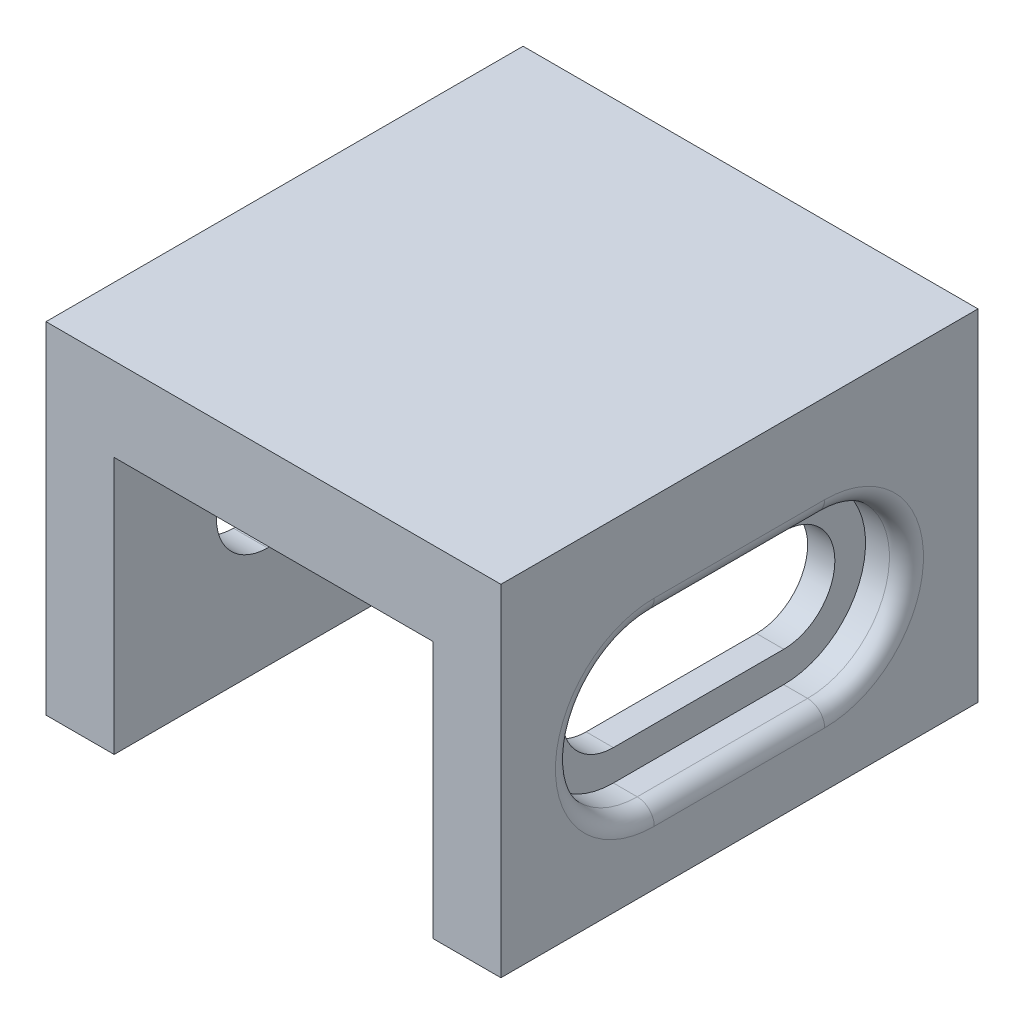
SolidWorks part; units mm, degrees
ref_plane "Front Plane" through (0, 0, 0) normal (0, 0, 1) x (1, 0, 0)
ref_plane "Top Plane" through (0, 0, 0) normal (0, 1, 0) x (1, 0, 0)
ref_plane "Right Plane" through (0, 0, 0) normal (1, 0, 0) x (0, 0, -1)
sketch "Sketch1" plane through (0, 0, 0) normal (0, 1, 0) x (1, 0, 0)
  line L1 (0, 0) -> (26.7, 0)
  line L2 (0, 0) -> (0, 28)
  line L3 (0, 28) -> (26.7, 28)
  line L4 (26.7, 0) -> (26.7, 28)
  dimension "D1" = 26.7
  dimension "D2" = 28
extrude "Boss-Extrude1" add sketch "Sketch1" along normal blind 20
sketch "Sketch2" plane through (0, 0, 0) normal (-1, 0, 0) x (0, 0, 1)
  line L0 (0, 20) -> (0, 0) construction
  line L1 (-28, 0) -> (0, 0) construction
  line L2 (-28, 20) -> (-28, 0) construction
  line L4 (-19, 12) -> (-9, 12)
  line L6 (-19, 6) -> (-9, 6)
  arc A0 (-9, 6) -> (-9, 12) centre (-9, 9) ccw
  arc A1 (-19, 12) -> (-19, 6) centre (-19, 9) ccw
  dimension "D1" = 6
  dimension "D4" = 9
  dimension "D6" = 6
  dimension "D2" = 9
  dimension "D5" = 9
extrude "Cut-Extrude1" cut sketch "Sketch2" against normal blind 27.5
sketch "Sketch3" plane through (0, 0, 0) normal (-1, 0, 0) x (0, 0, 1)
  line L1 (-19, 13.8) -> (-9, 13.8)
  line L3 (-19, 4.2) -> (-9, 4.2)
  arc A0 (-9, 4.2) -> (-9, 13.8) centre (-9, 9) ccw
  arc A1 (-19, 13.8) -> (-19, 4.2) centre (-19, 9) ccw
  point P1 (0, 0)
  point P4 (0, 0)
  point P5 (0, 0)
  dimension "D1" = 4.8
extrude "Cut-Extrude2" cut sketch "Sketch3" against normal blind 2
sketch "Sketch4" plane through (26.7, 0, 0) normal (1, 0, 0) x (0, 0, -1)
  line L1 (9, 13.8) -> (19, 13.8)
  line L3 (9, 4.2) -> (19, 4.2)
  arc A0 (9, 13.8) -> (9, 4.2) centre (9, 9) ccw
  arc A1 (19, 4.2) -> (19, 13.8) centre (19, 9) ccw
  dimension "D1" = 4.8
extrude "Cut-Extrude3" cut sketch "Sketch4" against normal blind 2.4
sketch "Sketch5" plane through (0, 0, 0) normal (0, 1, 0) x (1, 0, 0)
  line L0 (26.7, 28) -> (0, 28) construction
  line L1 (4, 28) -> (22.7, 28)
  line L2 (4, 28) -> (4, 0)
  line L3 (4, 0) -> (22.7, 0)
  line L4 (22.7, 28) -> (22.7, 0)
  line L5 (0, 0) -> (26.7, 0) construction
  line L6 (0, 28) -> (0, 0) construction
  line L7 (26.7, 0) -> (26.7, 28) construction
  dimension "D1" = 4
  dimension "D2" = 4
extrude "Cut-Extrude4" cut sketch "Sketch5" along normal blind 15.1
fillet "Fillet1" radius 1 8 edges at (0, 9, -23.8) (0, 13.8, -14) (0, 9, -4.2) (26.7, 9, -4.2) (26.7, 13.8, -14) (26.7, 9, -23.8) (0, 4.2, -14) (26.7, 4.2, -14)
